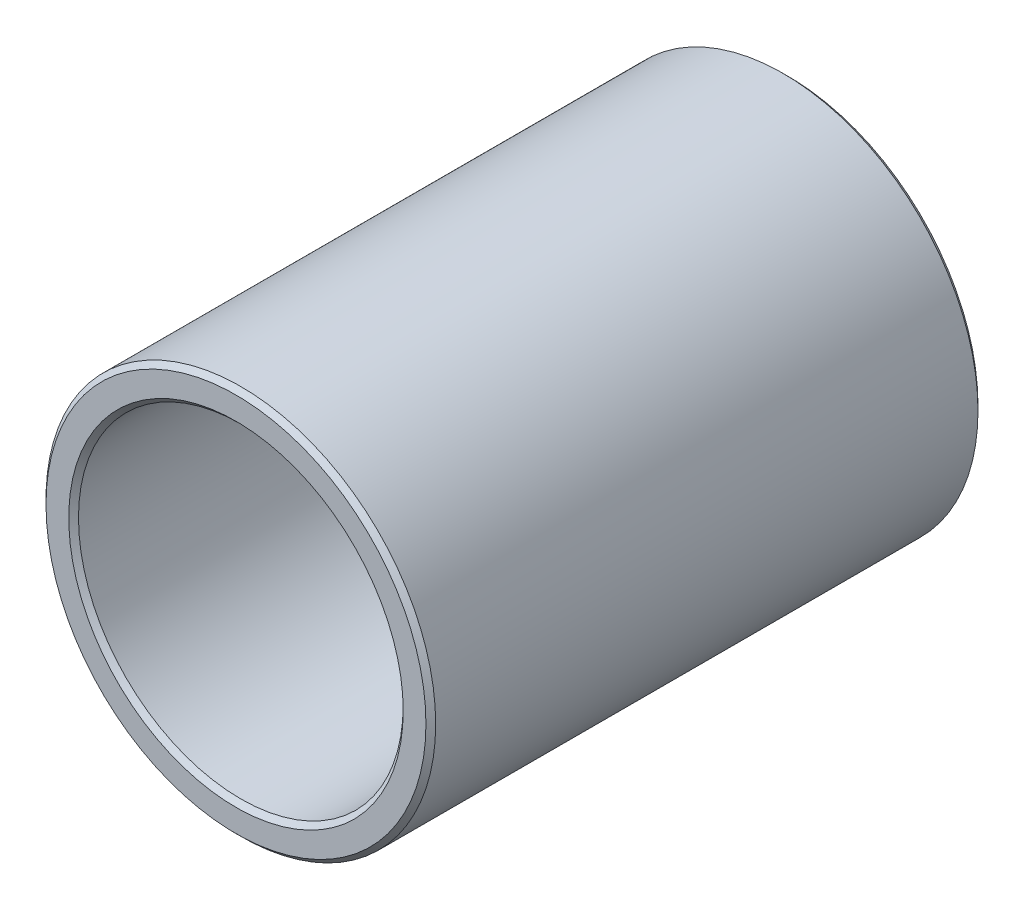
SolidWorks part; units mm, degrees
ref_plane "Piano frontale" through (0, 0, 0) normal (0, 0, 1) x (1, 0, 0)
ref_plane "Piano superiore" through (0, 0, 0) normal (0, 1, 0) x (1, 0, 0)
ref_plane "Piano destro" through (0, 0, 0) normal (1, 0, 0) x (0, 0, -1)
sketch "Schizzo1" plane through (0, 0, 0) normal (0, 0, 1) x (1, 0, 0)
  circle A0 centre (0, 0) radius 12
  circle A1 centre (0, 0) radius 10
extrude "Estrusione-Estrusione1" add sketch "Schizzo1" along normal blind 34
chamfer "Smusso1" distance 0.3 angle 45 4 edges at (10, 0, 0) (12, 0, 0) (10, 0, 34) (12, 0, 34)
